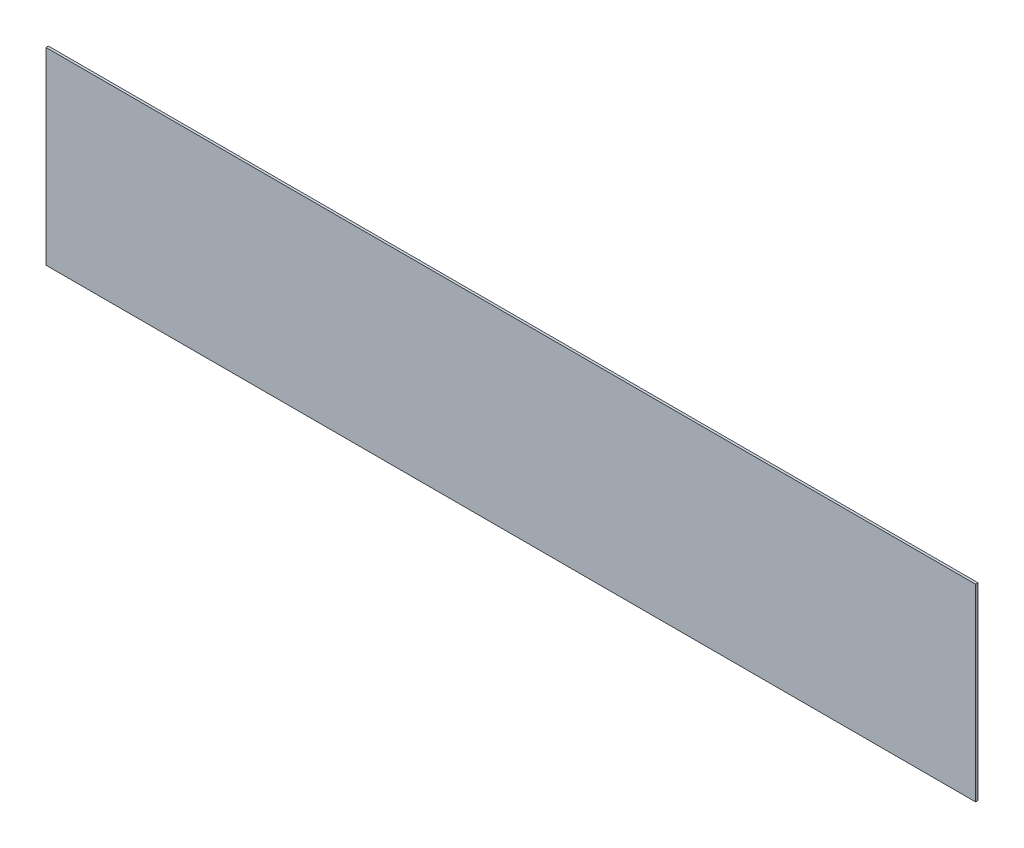
SolidWorks part; units mm, degrees
material "Acrylic (Medium-high impact)"
ref_plane "Front Plane" through (0, 0, 0) normal (0, 0, 1) x (1, 0, 0)
ref_plane "Top Plane" through (0, 0, 0) normal (0, 1, 0) x (1, 0, 0)
ref_plane "Right Plane" through (0, 0, 0) normal (1, 0, 0) x (0, 0, -1)
sketch "Sketch1" plane through (0, 0, 0) normal (0, 0, 1) x (1, 0, 0)
  line L1 (0, 0) -> (609.6, 0)
  line L2 (0, 0) -> (0, 123.6726)
  line L3 (0, 123.6726) -> (609.6, 123.6726)
  line L4 (609.6, 0) -> (609.6, 123.6726)
  dimension "D1" = 123.6726
  dimension "D2" = 609.6
extrude "Boss-Extrude1" add sketch "Sketch1" along normal blind 1.5875
